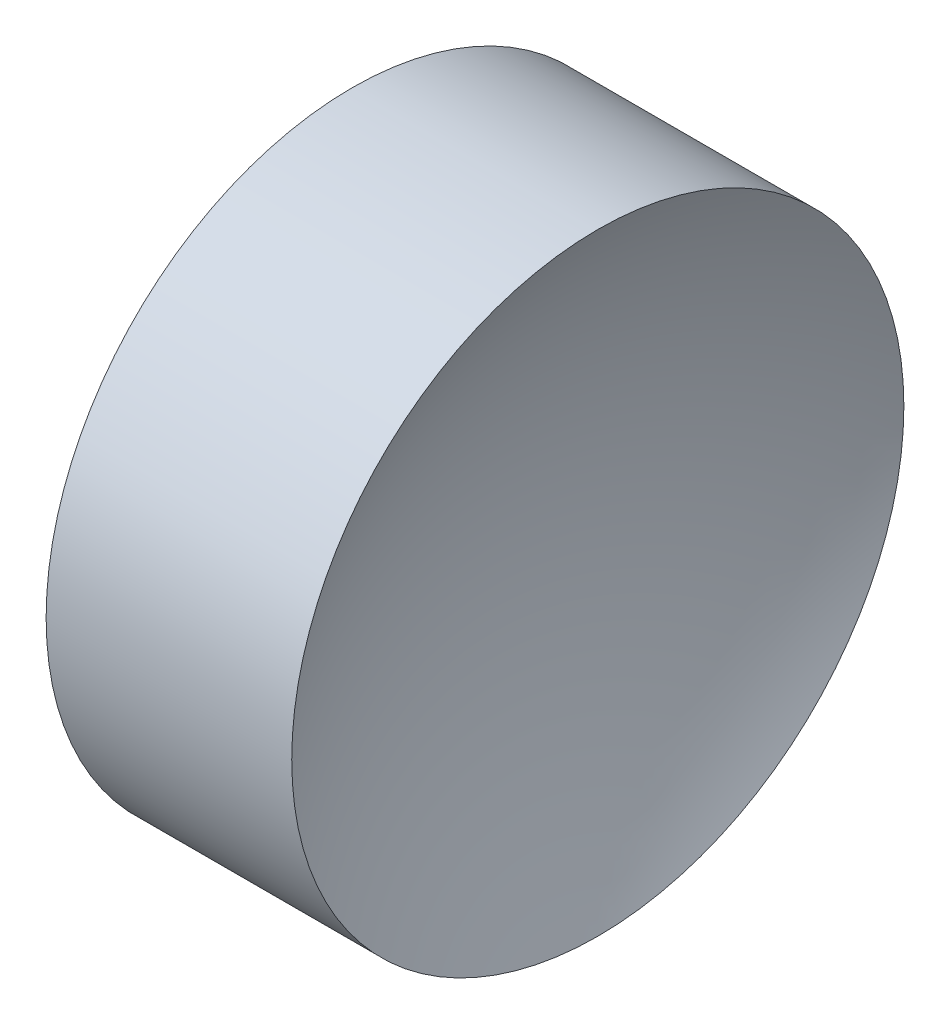
SolidWorks part; units mm, degrees
ref_plane "前视基准面" through (0, 0, 0) normal (0, 0, 1) x (1, 0, 0)
ref_plane "上视基准面" through (0, 0, 0) normal (0, 1, 0) x (1, 0, 0)
ref_plane "右视基准面" through (0, 0, 0) normal (1, 0, 0) x (0, 0, -1)
sketch "草图1" plane through (0, 0, 0) normal (0, 0, 1) x (1, 0, 0)
  line L0 (21.2249, 13.0445) -> (27.8323, 13.0445) construction
  line L1 (23.2743, 13.0445) -> (24.7743, 13.0445)
  line L3 (24.0243, 18.0445) -> (22.0182, 18.0445)
  line L4 (24.0243, 18.0445) -> (26.0303, 18.0445)
  arc A0 (26.0303, 18.0445) -> (24.7743, 13.0445) centre (35.3543, 13.0445) ccw
  arc A1 (23.2743, 13.0445) -> (22.0182, 18.0445) centre (12.6943, 13.0445) ccw
  dimension "D1" = 10.58
  dimension "D2" = 10.58
revolve "旋转1" add sketch "草图1" angle 360 about L0
